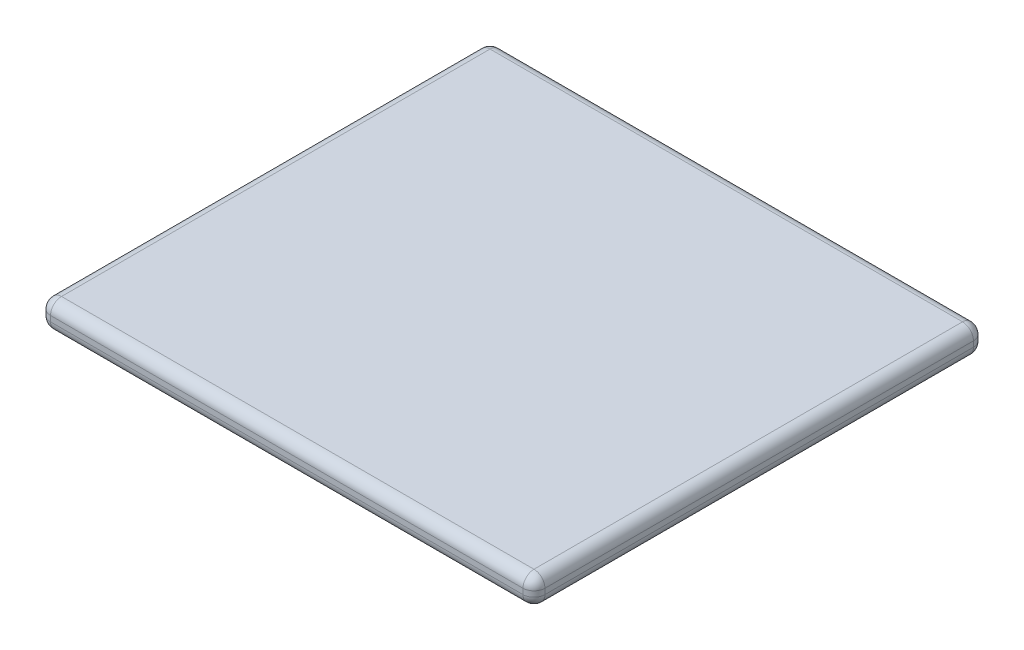
SolidWorks part; units mm, degrees
ref_plane "Front Plane" through (0, 0, 0) normal (0, 0, 1) x (1, 0, 0)
ref_plane "Top Plane" through (0, 0, 0) normal (0, 1, 0) x (1, 0, 0)
ref_plane "Right Plane" through (0, 0, 0) normal (1, 0, 0) x (0, 0, -1)
sketch "Sketch1" plane through (0, 0, 0) normal (0, 1, 0) x (1, 0, 0)
  line L1 (-205, 205) -> (245, 205)
  line L2 (-205, 205) -> (-205, -205)
  line L3 (-205, -205) -> (245, -205)
  line L4 (245, -205) -> (245, 205)
  dimension "D2" = 450
extrude "Boss-Extrude1" add sketch "Sketch1" along normal blind 25
fillet "Fillet1" radius 10 12 edges at (245, 12.5, -205) (-205, 12.5, -205) (-205, 12.5, 205) (245, 12.5, 205) (20, 25, 205) (-205, 25, 0) (20, 25, -205) (245, 25, 0) (20, 0, -205) (-205, 0, 0) (20, 0, 205) (245, 0, 0)
